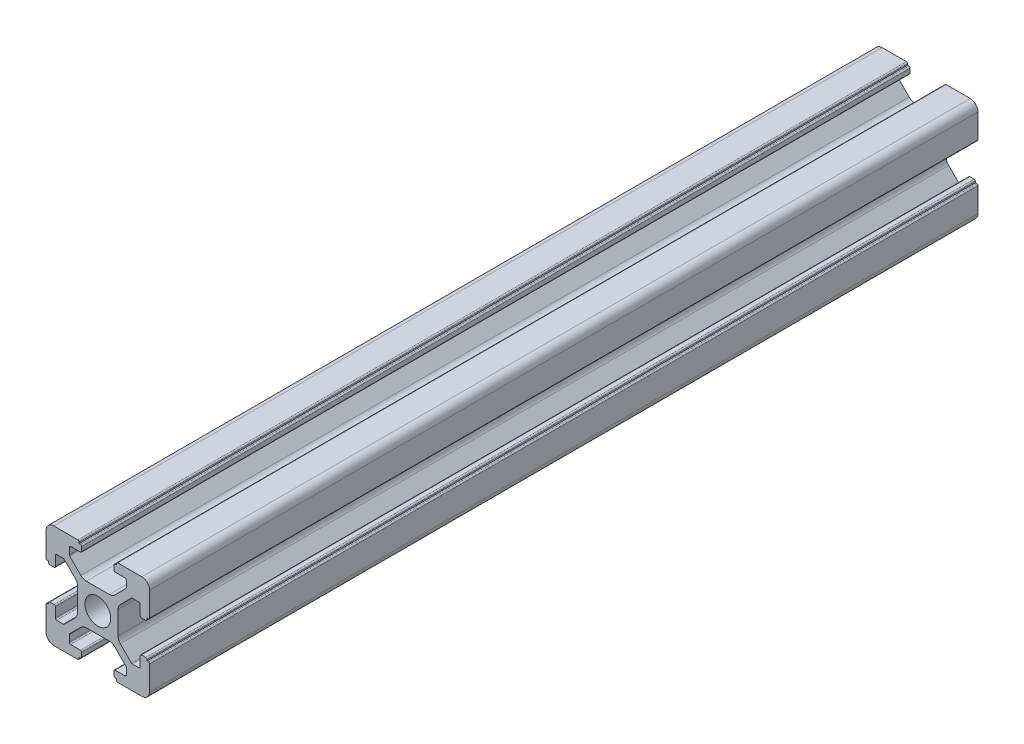
SolidWorks part; units mm, degrees
ref_plane "前视基准面" through (0, 0, 0) normal (0, 0, 1) x (1, 0, 0)
ref_plane "上视基准面" through (0, 0, 0) normal (0, 1, 0) x (1, 0, 0)
ref_plane "右视基准面" through (0, 0, 0) normal (1, 0, 0) x (0, 0, -1)
sketch "草图1" plane through (0, 0, 0) normal (0, 0, 1) x (1, 0, 0)
  line L0 (0, 0) -> (0, 5.5) construction
  line L1 (-8.5023, -10.0023) -> (-3.85, -10.0023)
  line L2 (-10.0023, -8.5023) -> (-10.0023, -3.85)
  line L3 (-8.5023, 10.0023) -> (-3.85, 10.0023)
  line L4 (10.0023, -8.5023) -> (10.0023, -3.85)
  line L5 (-10.0023, -10.0023) -> (10.0023, 10.0023) construction
  line L6 (-10.0023, 10.0023) -> (10.0023, -10.0023) construction
  line L7 (-2.218, -3.9) -> (2.218, -3.9)
  line L8 (-3.9, -2.218) -> (-3.9, 2.218)
  line L9 (-2.218, 3.9) -> (2.218, 3.9)
  line L10 (3.9, -2.218) -> (3.9, 2.218)
  line L11 (-3.9, -3.9) -> (3.9, 3.9) construction
  line L12 (-3.9, 3.9) -> (3.9, -3.9) construction
  line L13 (-5.25, -8.2) -> (-3.35, -8.2)
  line L14 (-8.2, -5.25) -> (-8.2, -3.35)
  line L15 (-5.25, 8.2) -> (-3.35, 8.2)
  line L16 (8.2, -5.25) -> (8.2, -3.35)
  line L17 (-8.2, -8.2) -> (8.2, 8.2) construction
  line L18 (-8.2, 8.2) -> (8.2, -8.2) construction
  line L19 (-7.95, 5.5) -> (-6.6642, 5.5)
  line L20 (0, 0) -> (5.5, 0) construction
  line L23 (-5.5, 7.95) -> (-5.5, 6.6642)
  line L26 (0, 0) -> (-0.5303, 0.5303)
  line L27 (3.2787, 4.3393) -> (5.4268, 6.4874)
  line L28 (0, 0) -> (0.5303, -0.5303)
  line L29 (5.5, 6.6642) -> (5.5, 7.95)
  line L30 (4.3393, 3.2787) -> (6.4874, 5.4268)
  line L31 (6.6642, 5.5) -> (7.95, 5.5)
  line L32 (4.3393, -3.2787) -> (6.4874, -5.4268)
  line L33 (3.2787, -4.3393) -> (5.4268, -6.4874)
  line L34 (-3.2787, -4.3393) -> (-5.4268, -6.4874)
  line L35 (-4.3393, -3.2787) -> (-6.4874, -5.4268)
  line L36 (-4.3393, 3.2787) -> (-6.4874, 5.4268)
  line L37 (-3.2787, 4.3393) -> (-5.4268, 6.4874)
  line L38 (3.1, -8.45) -> (3.1, -9.2523)
  line L39 (8.45, 3.1) -> (9.2523, 3.1)
  line L40 (-5.5, -6.6642) -> (-5.5, -7.95)
  line L41 (-6.6642, -5.5) -> (-7.95, -5.5)
  line L42 (5.5, -6.6642) -> (5.5, -7.95)
  line L43 (6.6642, -5.5) -> (7.95, -5.5)
  line L44 (9.2523, -3.1) -> (8.45, -3.1)
  line L46 (10.0023, 3.85) -> (10.0023, 8.5023)
  line L47 (8.2, 3.35) -> (8.2, 5.25)
  line L48 (-3.1, -9.2523) -> (-3.1, -8.45)
  line L49 (-8.45, -3.1) -> (-9.2523, -3.1)
  line L50 (-9.2523, 3.1) -> (-8.45, 3.1)
  line L51 (-3.1, 8.45) -> (-3.1, 9.2523)
  line L52 (3.1, 9.2523) -> (3.1, 8.45)
  line L53 (3.85, 10.0023) -> (8.5023, 10.0023)
  line L54 (3.35, 8.2) -> (5.25, 8.2)
  line L55 (-10.0023, 3.85) -> (-10.0023, 8.5023)
  line L56 (-8.2, 3.35) -> (-8.2, 5.25)
  line L57 (3.35, -8.2) -> (5.25, -8.2)
  line L58 (3.85, -10.0023) -> (8.5023, -10.0023)
  line L59 (9.7523, -3.6) -> (9.5023, -3.6)
  line L61 (9.7523, 3.6) -> (9.5023, 3.6)
  line L62 (9.5023, -3.6) -> (9.5023, -3.35)
  line L63 (3.6, -9.7523) -> (3.6, -9.5023)
  line L64 (3.35, -9.5023) -> (3.6, -9.5023)
  line L65 (9.5023, 3.35) -> (9.5023, 3.6)
  line L66 (-3.6, -9.5023) -> (-3.35, -9.5023)
  line L67 (-3.6, -9.7523) -> (-3.6, -9.5023)
  line L68 (-9.7523, -3.6) -> (-9.5023, -3.6)
  line L69 (-9.5023, -3.35) -> (-9.5023, -3.6)
  line L70 (-9.5023, 3.6) -> (-9.5023, 3.35)
  line L71 (-9.7523, 3.6) -> (-9.5023, 3.6)
  line L72 (-3.6, 9.7523) -> (-3.6, 9.5023)
  line L73 (-3.35, 9.5023) -> (-3.6, 9.5023)
  line L74 (3.6, 9.5023) -> (3.35, 9.5023)
  line L75 (3.6, 9.7523) -> (3.6, 9.5023)
  circle A0 centre (0, 0) radius 2.5
  arc A1 (10.0023, 8.5023) -> (8.5023, 10.0023) centre (8.5023, 8.5023) ccw
  arc A2 (8.5023, -10.0023) -> (10.0023, -8.5023) centre (8.5023, -8.5023) ccw
  arc A3 (-10.0023, -8.5023) -> (-8.5023, -10.0023) centre (-8.5023, -8.5023) ccw
  arc A4 (-10.0023, 8.5023) -> (-8.5023, 10.0023) centre (-8.5023, 8.5023) cw
  arc A5 (-9.5023, -3.35) -> (-9.2523, -3.1) centre (-9.2523, -3.35) cw
  arc A6 (-9.7523, -3.6) -> (-10.0023, -3.85) centre (-9.7523, -3.85) ccw
  arc A7 (-8.45, -3.1) -> (-8.2, -3.35) centre (-8.45, -3.35) cw
  arc A8 (-7.95, -5.5) -> (-8.2, -5.25) centre (-7.95, -5.25) cw
  arc A9 (-6.4874, -5.4268) -> (-6.6642, -5.5) centre (-6.6642, -5.25) cw
  arc A10 (-5.4268, -6.4874) -> (-5.5, -6.6642) centre (-5.25, -6.6642) ccw
  arc A11 (-5.5, -7.95) -> (-5.25, -8.2) centre (-5.25, -7.95) ccw
  arc A12 (-3.6, -9.7523) -> (-3.85, -10.0023) centre (-3.85, -9.7523) cw
  arc A13 (-3.35, -9.5023) -> (-3.1, -9.2523) centre (-3.35, -9.2523) ccw
  arc A14 (-3.1, -8.45) -> (-3.35, -8.2) centre (-3.35, -8.45) ccw
  arc A15 (3.1, -8.45) -> (3.35, -8.2) centre (3.35, -8.45) cw
  arc A16 (5.5, -7.95) -> (5.25, -8.2) centre (5.25, -7.95) cw
  arc A17 (5.4268, -6.4874) -> (5.5, -6.6642) centre (5.25, -6.6642) cw
  arc A18 (6.4874, -5.4268) -> (6.6642, -5.5) centre (6.6642, -5.25) ccw
  arc A19 (7.95, -5.5) -> (8.2, -5.25) centre (7.95, -5.25) ccw
  arc A20 (8.45, -3.1) -> (8.2, -3.35) centre (8.45, -3.35) ccw
  arc A21 (9.5023, -3.35) -> (9.2523, -3.1) centre (9.2523, -3.35) ccw
  arc A22 (9.7523, -3.6) -> (10.0023, -3.85) centre (9.7523, -3.85) cw
  arc A23 (3.35, -9.5023) -> (3.1, -9.2523) centre (3.35, -9.2523) cw
  arc A24 (3.6, -9.7523) -> (3.85, -10.0023) centre (3.85, -9.7523) ccw
  arc A25 (7.95, 5.5) -> (8.2, 5.25) centre (7.95, 5.25) cw
  arc A26 (8.2, 3.35) -> (8.45, 3.1) centre (8.45, 3.35) ccw
  arc A27 (9.5023, 3.35) -> (9.2523, 3.1) centre (9.2523, 3.35) cw
  arc A28 (9.7523, 3.6) -> (10.0023, 3.85) centre (9.7523, 3.85) ccw
  arc A29 (6.6642, 5.5) -> (6.4874, 5.4268) centre (6.6642, 5.25) ccw
  arc A30 (5.4268, 6.4874) -> (5.5, 6.6642) centre (5.25, 6.6642) ccw
  arc A31 (5.5, 7.95) -> (5.25, 8.2) centre (5.25, 7.95) ccw
  arc A32 (3.1, 8.45) -> (3.35, 8.2) centre (3.35, 8.45) ccw
  arc A33 (3.6, 9.7523) -> (3.85, 10.0023) centre (3.85, 9.7523) cw
  arc A34 (3.35, 9.5023) -> (3.1, 9.2523) centre (3.35, 9.2523) ccw
  arc A35 (-9.7523, 3.6) -> (-10.0023, 3.85) centre (-9.7523, 3.85) cw
  arc A36 (-9.5023, 3.35) -> (-9.2523, 3.1) centre (-9.2523, 3.35) ccw
  arc A37 (-8.45, 3.1) -> (-8.2, 3.35) centre (-8.45, 3.35) ccw
  arc A38 (-8.2, 5.25) -> (-7.95, 5.5) centre (-7.95, 5.25) cw
  arc A39 (-6.4874, 5.4268) -> (-6.6642, 5.5) centre (-6.6642, 5.25) ccw
  arc A40 (-5.4268, 6.4874) -> (-5.5, 6.6642) centre (-5.25, 6.6642) cw
  arc A41 (-5.5, 7.95) -> (-5.25, 8.2) centre (-5.25, 7.95) cw
  arc A42 (-3.1, 8.45) -> (-3.35, 8.2) centre (-3.35, 8.45) cw
  arc A43 (-3.1, 9.2523) -> (-3.35, 9.5023) centre (-3.35, 9.2523) ccw
  arc A44 (-3.6, 9.7523) -> (-3.85, 10.0023) centre (-3.85, 9.7523) ccw
  arc A45 (-4.3393, 3.2787) -> (-3.9, 2.218) centre (-5.4, 2.218) cw
  arc A46 (-3.2787, 4.3393) -> (-2.218, 3.9) centre (-2.218, 5.4) ccw
  arc A47 (3.2787, 4.3393) -> (2.218, 3.9) centre (2.218, 5.4) cw
  arc A48 (4.3393, 3.2787) -> (3.9, 2.218) centre (5.4, 2.218) ccw
  arc A49 (4.3393, -3.2787) -> (3.9, -2.218) centre (5.4, -2.218) cw
  arc A50 (3.2787, -4.3393) -> (2.218, -3.9) centre (2.218, -5.4) ccw
  arc A51 (-4.3393, -3.2787) -> (-3.9, -2.218) centre (-5.4, -2.218) ccw
  arc A52 (-2.218, -3.9) -> (-3.2787, -4.3393) centre (-2.218, -5.4) ccw
  point P0 (0, 0)
  point P7 (10.0023, 0)
  point P62 (0, 0)
  point P76 (0, 0)
  point P92 (-8.2, -5.5)
  point P99 (0, 0)
  point P106 (-5.5, -8.2)
  point P117 (5.5, -8.2)
  point P124 (8.2, -5.5)
  point P137 (8.2, 5.5)
  point P140 (8.2, 3.1)
  point P147 (6.5607, 5.5)
  point P152 (5.5, 8.2)
  point P167 (-8.2, 5.5)
  point P174 (-5.5, 8.2)
  dimension "D1" = 1.5
  dimension "D5" = 0.25
  dimension "D6" = 1.5
  dimension "D2" = 4
  dimension "D3" = 4
  dimension "D4" = 4
extrude "凸台-拉伸1" add sketch "草图1" along normal blind 160 contours A52 L7 A50 L33 A17 L42 A16 L57 A15 L38 A23 L64 L63 A24 L58 A2 L4 A22 L59 L62 A21 L44 A20 L16 A19 L43 A18 L32 A49 L10 A48 L30 A29 L31 A25 L47 A26 L39 A27 L65 L61 A28 L46 A1 L53 A33 L75 L74 A34 L52 A32
ref_plane "Plane1" through (0, 0, 80) normal (0, 0, -1) x (-1, 0, 0)
